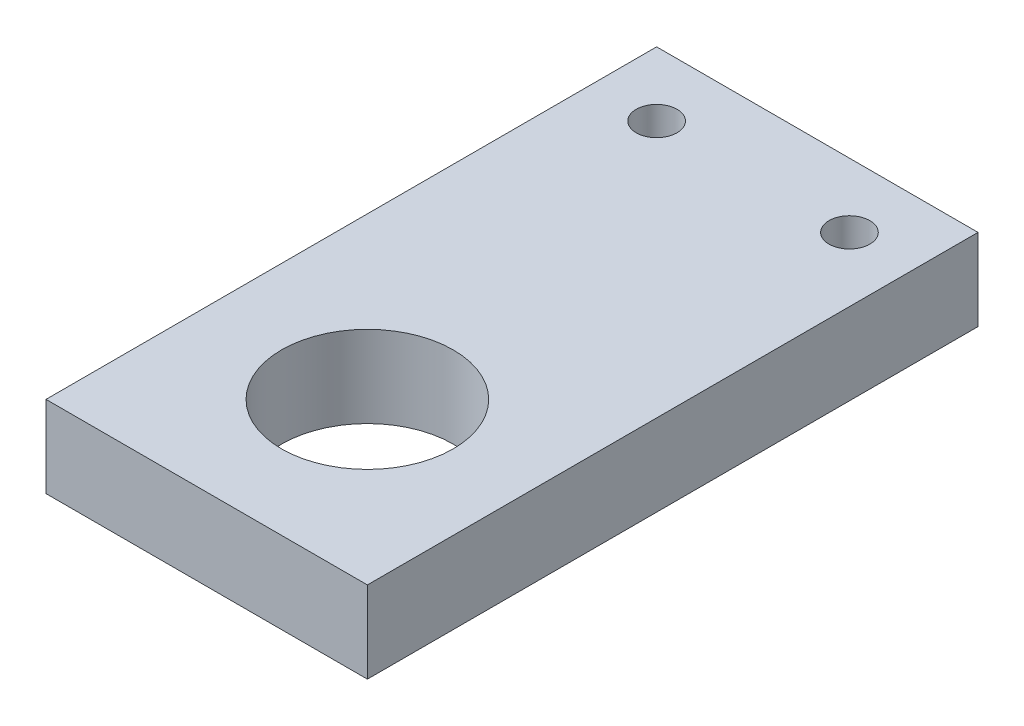
SolidWorks part; units mm, degrees
ref_plane "Front Plane" through (0, 0, 0) normal (0, 0, 1) x (1, 0, 0)
ref_plane "Top Plane" through (0, 0, 0) normal (0, 1, 0) x (1, 0, 0)
ref_plane "Right Plane" through (0, 0, 0) normal (1, 0, 0) x (0, 0, -1)
sketch "Sketch1" plane through (0, 0, 0) normal (0, 1, 0) x (1, 0, 0)
  line L1 (0, 0) -> (25, 0)
  line L2 (0, 0) -> (0, 47.5)
  line L3 (0, 47.5) -> (25, 47.5)
  line L4 (25, 0) -> (25, 47.5)
  circle A0 centre (12.5, 12.5) radius 6.675
  dimension "D3" = 13.35
  dimension "D1" = 12.5
  dimension "D2" = 25
  dimension "D4" = 12.5
  dimension "D5" = 35
extrude "Boss-Extrude1" add sketch "Sketch1" along normal blind 6.35
sketch "Sketch2" plane through (0, 6.35, 0) normal (0, 1, 0) x (1, 0, 0)
  line L0 (25, 47.5) -> (0, 47.5) construction
  line L1 (25, 0) -> (25, 47.5) construction
  line L2 (12.5, 47.5) -> (12.5, 31.2398) construction
  circle A0 centre (20, 42.5) radius 1.5875
  circle A1 centre (5, 42.5) radius 1.5875
  dimension "D1" = 3.175
  dimension "D2" = 5
  dimension "D3" = 5
extrude "Cut-Extrude1" cut sketch "Sketch2" against normal up to next
